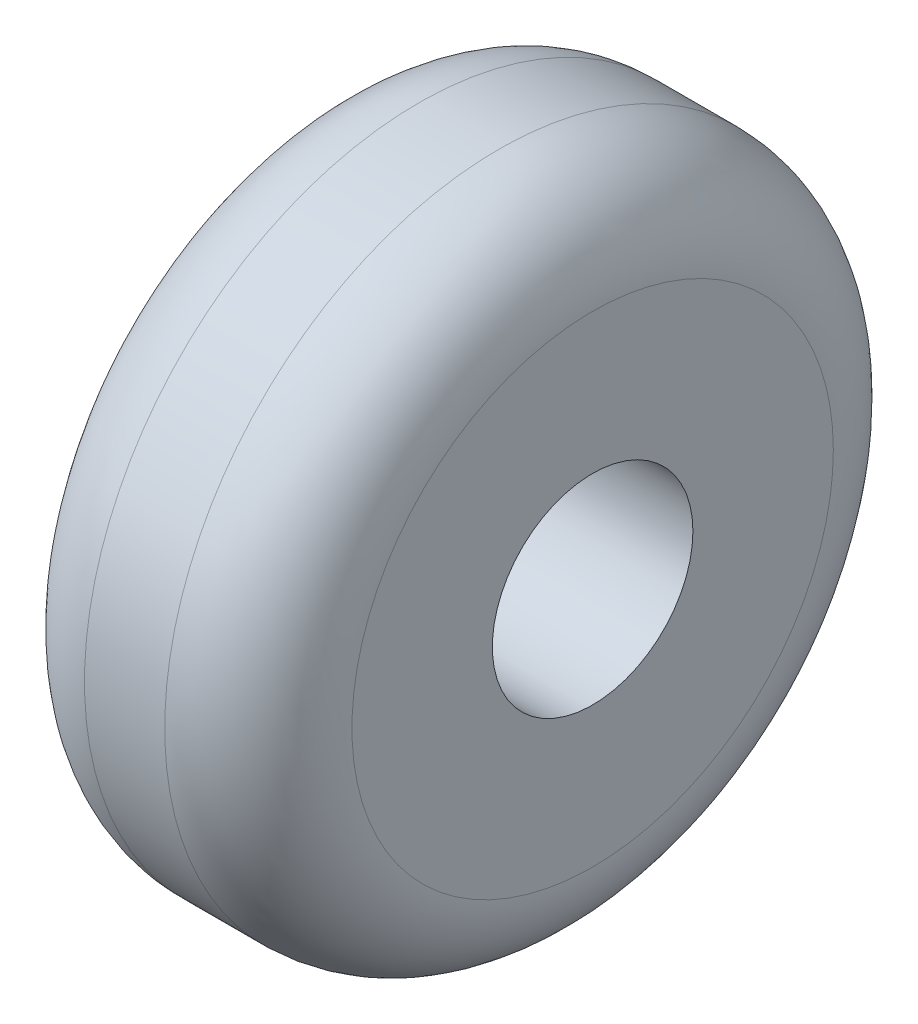
SolidWorks part; units mm, degrees
ref_plane "Front Plane" through (0, 0, 0) normal (0, 0, 1) x (1, 0, 0)
ref_plane "Top Plane" through (0, 0, 0) normal (0, 1, 0) x (1, 0, 0)
ref_plane "Right Plane" through (0, 0, 0) normal (1, 0, 0) x (0, 0, -1)
sketch "Sketch1" plane through (0, 0, 0) normal (1, 0, 0) x (0, 0, -1)
  circle A0 centre (0, 0) radius 2.5
  circle A1 centre (0, 0) radius 0.75
  dimension "D1" = 1.5
  dimension "D2" = 5
extrude "Boss-Extrude1" add sketch "Sketch1" along normal mid plane 2
fillet "Fillet1" radius 0.7 2 edges at (-1, 0, -2.5) (1, 0, -2.5)
